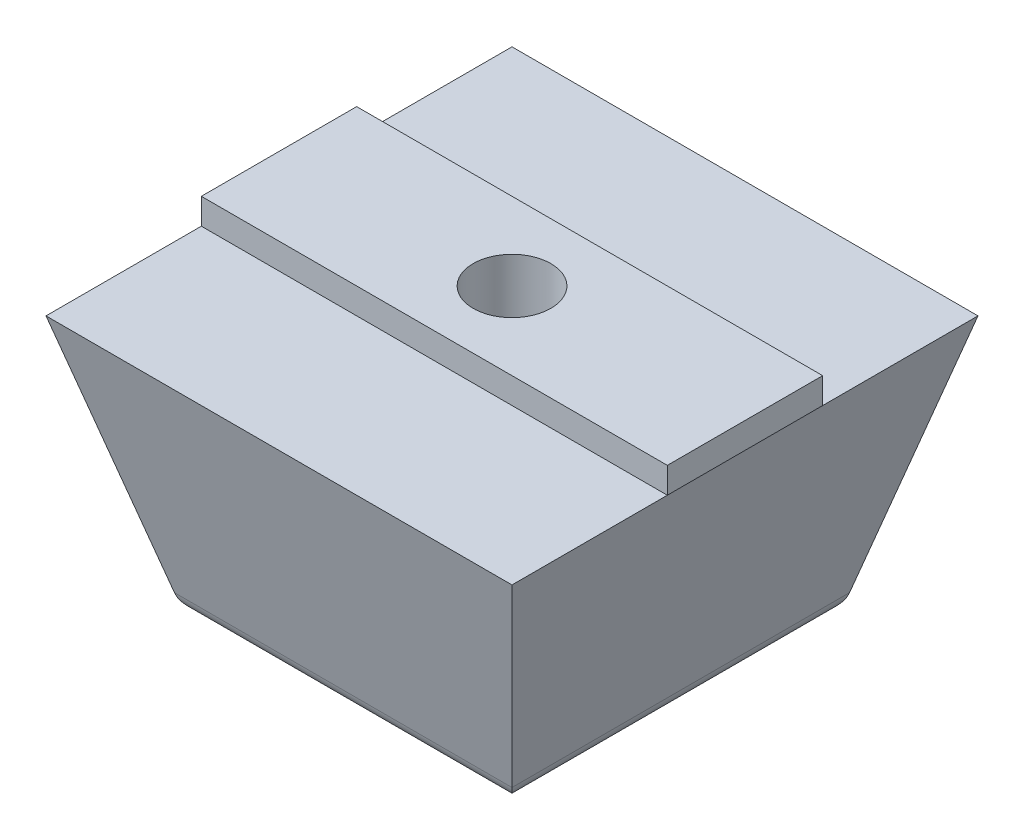
SolidWorks part; units mm, degrees
ref_plane "Front Plane" through (0, 0, 0) normal (0, 0, 1) x (1, 0, 0)
ref_plane "Top Plane" through (0, 0, 0) normal (0, 1, 0) x (1, 0, 0)
ref_plane "Right Plane" through (0, 0, 0) normal (1, 0, 0) x (0, 0, -1)
sketch "Sketch1" plane through (0, 0, 0) normal (0, 1, 0) x (1, 0, 0)
  line L1 (-9, -9) -> (9, -9)
  line L2 (-9, -9) -> (-9, 9)
  line L3 (-9, 9) -> (9, 9)
  line L4 (9, -9) -> (9, 9)
  line L5 (-9, -9) -> (9, 9) construction
  line L6 (-9, 9) -> (9, -9) construction
  point P0 (0, 0)
  dimension "D1" = 18
  dimension "D2" = 18
extrude "Boss-Extrude1" add sketch "Sketch1" against normal blind 10 draft 15
sketch "Sketch5" plane through (0, 0, 0) normal (0, 1, 0) x (1, 0, 0)
  line L0 (9, -9) -> (9, 9) construction
  line L1 (-9, -3) -> (9, -3)
  line L2 (-9, -3) -> (-9, 3)
  line L3 (-9, 3) -> (9, 3)
  line L4 (9, -3) -> (9, 3)
  line L5 (-9, -3) -> (9, 3) construction
  line L6 (-9, 3) -> (9, -3) construction
  point P0 (0, 0)
  dimension "D1" = 6
extrude "Boss-Extrude3" add sketch "Sketch5" along normal blind 3
fillet "Fillet2" radius 1 2 edges at (0, 3, 3) (0, 3, -3)
sketch "Sketch6" plane through (0, 3, 0) normal (0, 1, 0) x (1, 0, 0)
  circle A0 centre (0, 0) radius 1.5
  dimension "D1" = 3
extrude "Cut-Extrude3" cut sketch "Sketch6" against normal up to next
sketch "Sketch7" plane through (0, -10, 0) normal (0, -1, 0) x (1, 0, 0)
  circle A0 centre (0, 0) radius 3
  dimension "D1" = 6
extrude "Cut-Extrude4" cut sketch "Sketch7" against normal offset from surface (8 mm away) 2 up to face at (-2.25, 0, 6)
sketch "Sketch9" plane through (0, 3, 0) normal (0, 1, 0) x (1, 0, 0)
  line L0 (9, 3) -> (-9, 3) construction
  line L1 (-10, -3) -> (10, -3)
  line L2 (-10, -3) -> (-10, 3)
  line L3 (-10, 3) -> (10, 3)
  line L4 (10, -3) -> (10, 3)
  line L5 (-10, -3) -> (10, 3) construction
  line L6 (-10, 3) -> (10, -3) construction
  point P0 (0, 0)
  dimension "D1" = 20
extrude "Cut-Extrude5" cut sketch "Sketch9" against normal blind 2
fillet "Fillet4" radius 1 4 edges at (6.3205, -10, 0) (0, -10, -6.3205) (-6.3205, -10, 0) (0, -10, 6.3205)
sketch "Sketch10" plane through (0, -2, 0) normal (0, -1, 0) x (1, 0, 0)
  circle A0 centre (0, 0) radius 3 construction
  circle A1 centre (0, 0) radius 3
extrude "Boss-Extrude4" [suppressed] add sketch "Sketch10" against normal blind 0.6
